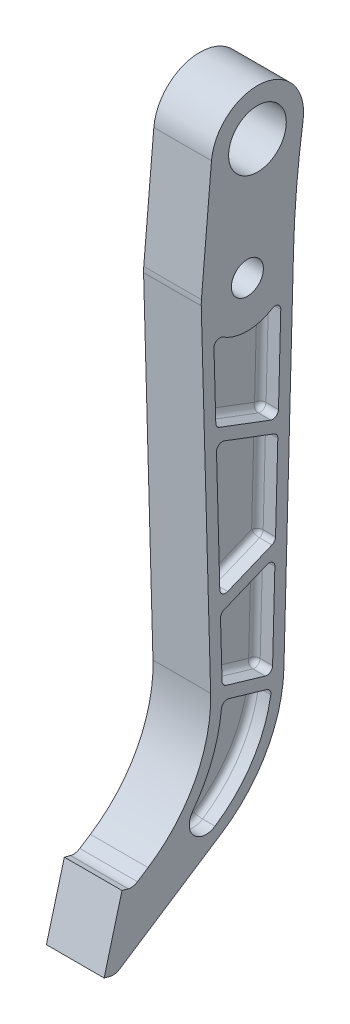
SolidWorks part; units mm, degrees
ref_plane "Front Plane" through (0, 0, 0) normal (0, 0, 1) x (1, 0, 0)
ref_plane "Top Plane" through (0, 0, 0) normal (0, 1, 0) x (1, 0, 0)
ref_plane "Right Plane" through (0, 0, 0) normal (1, 0, 0) x (0, 0, -1)
sketch "Sketch1" plane through (0, 0, 0) normal (1, 0, 0) x (0, 0, -1)
  line L0 (-25.3903, -0.7003) -> (-20.2239, -188.0148)
  line L1 (25.4, 0) -> (20.123, -196.1257)
  line L2 (0, 0) -> (-78.888, -294.4142) construction
  line L3 (0, 0) -> (0, -294.4142) construction
  line L4 (0, -294.4142) -> (-78.888, -294.4142) construction
  line L5 (-60.5169, -257.7014) -> (-54.6821, -253.8847)
  line L6 (-78.888, -294.4142) -> (-75.4975, -295.3227)
  line L7 (-78.888, -294.4142) -> (-69.027, -257.6124)
  line L8 (-69.027, -257.6124) -> (-65.6365, -258.5209)
  line L9 (-72.7544, -296.0577) -> (-62.8934, -259.2559) construction
  line L10 (-70.3779, -294.5031) -> (-14.3366, -257.8451)
  line L11 (0, 0) -> (5.5555, 63.5) construction
  line L12 (0, 0) -> (25.4, 0) construction
  line L13 (5.5555, 63.5) -> (5.5555, 0) construction
  line L14 (-19.7478, 65.7138) -> (-25.3033, 2.2138)
  circle A0 centre (0, 0) radius 8.8004
  arc A2 (-54.6821, -253.8847) -> (-20.2239, -188.0148) centre (-96.395, -190.1158) ccw
  arc A3 (-14.3366, -257.8451) -> (20.123, -196.1257) centre (-56.0494, -194.0762) ccw
  arc A4 (-70.3779, -294.5031) -> (-75.4975, -295.3227) centre (-73.854, -289.1891) cw
  arc A5 (-60.5169, -257.7014) -> (-65.6365, -258.5209) centre (-63.993, -252.3873) cw
  arc A8 (30.6732, 59.7236) -> (25.4, 0) centre (515.6373, -13.1904) ccw
  arc A9 (30.6732, 59.7236) -> (-19.7478, 65.7138) centre (5.5555, 63.5) ccw
  circle A10 centre (5.5555, 63.5) radius 15.875
  arc A11 (-25.3033, 2.2138) -> (-25.3903, -0.7003) centre (0, 0) ccw
  point P17 (-19.05, -230.5769)
  point P20 (19.05, -236.0062)
  dimension "D1" = 17.6007
  dimension "D2" = 25.4
  dimension "D7" = 76.2
  dimension "D8" = 76.2
  dimension "D12" = 6.35
  dimension "D13" = 6.35
  dimension "D14" = 25.4
  dimension "D17" = 31.75
  dimension "D3" = 304.8
  dimension "D4" = 15
  dimension "D5" = 38.1
  dimension "D6" = 6.35
  dimension "D9" = 19.05
  dimension "D10" = 19.05
  dimension "D11" = 25.4
  dimension "D15" = 5
  dimension "D16" = 63.5
  dimension "D18" = 25.4
extrude "Boss-Extrude1" add sketch "Sketch1" along normal mid plane 31.75
sketch "Sketch2" plane through (15.875, 0, 0) normal (1, 0, 0) x (0, 0, -1)
  line L0 (-11.6603, -188.4901) -> (9.8183, -194.7936)
  line L1 (-18.3877, -24.2757) -> (18.3947, -24.2692) construction
  line L2 (0.0035, -24.2725) -> (-0.921, -191.6419) construction
  line L3 (-16.082, -107.8709) -> (16.1405, -108.0489) construction
  line L4 (15.5153, -131.2875) -> (16.7658, -84.8102)
  line L5 (-15.1742, -141.2921) -> (-16.9898, -74.4496)
  line L6 (-10.7935, -144.1426) -> (13.5483, -134.1388)
  line L7 (-12.6932, -71.3935) -> (14.7147, -81.7549)
  line L8 (-15.3313, -63.6076) -> (12.8308, -74.2541)
  line L9 (-14.77, -63.8198) -> (19.139, -76.6389) construction
  line L10 (-18.3877, -24.2757) -> (-17.3823, -60.7253)
  line L11 (17.1274, -71.3697) -> (18.3947, -24.2692)
  line L12 (-12.8189, -151.8403) -> (10.761, -142.1497)
  line L13 (-12.9293, -151.8857) -> (17.6096, -139.3351) construction
  line L14 (-14.7858, -154.8646) -> (-13.94, -185.5312)
  line L15 (13.8862, -191.8325) -> (15.1417, -145.1717)
  line L16 (-19.0428, -0.5252) -> (-13.8763, -187.8398)
  line L17 (-51.206, -259.1988) -> (-57.0408, -263.0155)
  line L18 (-64.4537, -265.0789) -> (-70.2892, -286.8572)
  line L19 (-70.2892, -286.8572) -> (-17.8126, -252.5311)
  line L20 (13.7753, -195.9549) -> (19.0523, 0.1708)
  line L21 (-13.422, 65.1603) -> (-18.9775, 1.6603)
  line L22 (-18.3877, -24.2757) -> (-13.8763, -187.8398) construction
  line L26 (13.7753, -195.9549) -> (18.3947, -24.2692) construction
  line L28 (-15.3431, -146.0124) -> (15.1958, -133.4617) construction
  line L29 (-17.0155, -69.7595) -> (16.8936, -82.5786) construction
  line L30 (-10.1952, -195.5379) -> (10.6667, -201.6604)
  line L31 (-13.4485, -194.5832) -> (8.0301, -200.8866) construction
  arc A0 (-30.1717, -239.4004) -> (-17.8126, -252.5311) centre (-22.8255, -244.8676) ccw
  arc A1 (9.8183, -194.7936) -> (13.8862, -191.8325) centre (10.7124, -191.7471) ccw
  arc A2 (-11.6603, -188.4901) -> (-13.94, -185.5312) centre (-10.7662, -185.4436) cw
  arc A3 (-12.8189, -151.8403) -> (-14.7858, -154.8646) centre (-11.6121, -154.777) ccw
  arc A4 (10.761, -142.1497) -> (15.1417, -145.1717) centre (11.9678, -145.0863) cw
  arc A5 (15.5153, -131.2875) -> (13.5483, -134.1388) centre (12.3414, -131.2021) cw
  arc A6 (-15.1742, -141.2921) -> (-10.7935, -144.1426) centre (-12.0004, -141.2059) ccw
  arc A8 (-13.5235, -21.5006) -> (13.5297, -21.4967) centre (0, 0) ccw
  arc A9 (-25.3033, 2.2138) -> (-25.3903, -0.7003) centre (0, 0) ccw construction
  arc A10 (18.3947, -24.2692) -> (13.5297, -21.4967) centre (15.2209, -24.1838) ccw
  arc A11 (-18.3877, -24.2757) -> (-13.5235, -21.5006) centre (-15.2139, -24.1882) cw
  arc A14 (-18.9775, 1.6603) -> (-19.0428, -0.5252) centre (0, 0) ccw
  arc A15 (-51.206, -259.1988) -> (-13.8763, -187.8398) centre (-96.395, -190.1158) ccw
  arc A16 (-64.4537, -265.0789) -> (-57.0408, -263.0155) centre (-63.993, -252.3873) ccw
  arc A17 (-17.8126, -252.5311) -> (13.7753, -195.9549) centre (-56.0494, -194.0762) ccw
  arc A18 (24.3938, 60.6677) -> (19.0523, 0.1708) centre (515.6373, -13.1904) ccw
  arc A19 (24.3938, 60.6677) -> (-13.422, 65.1603) centre (5.5555, 63.5) ccw
  arc A21 (-30.1717, -239.4004) -> (-13.8763, -187.8398) centre (-96.395, -190.1158) ccw construction
  arc A23 (-17.8126, -252.5311) -> (13.7753, -195.9549) centre (-56.0494, -194.0762) ccw construction
  arc A24 (16.7658, -84.8102) -> (14.7147, -81.7549) centre (13.5919, -84.7248) ccw
  arc A25 (-12.6932, -71.3935) -> (-16.9898, -74.4496) centre (-13.8159, -74.3634) ccw
  arc A26 (12.8308, -74.2541) -> (17.1274, -71.3697) centre (13.9536, -71.2843) ccw
  arc A27 (-15.3313, -63.6076) -> (-17.3823, -60.7253) centre (-14.2086, -60.6377) cw
  arc A28 (-14.2488, -198.2708) -> (-30.1717, -239.4004) centre (-96.395, -190.1158) cw
  arc A29 (12.907, -205.2132) -> (-17.8126, -252.5311) centre (-56.0494, -194.0762) cw
  arc A30 (10.6667, -201.6604) -> (12.907, -205.2132) centre (9.7727, -204.7069) cw
  arc A31 (-10.1952, -195.5379) -> (-14.2488, -198.2708) centre (-11.0893, -198.5844) ccw
  point P14 (-0.4587, -107.9572)
  point P21 (16.1405, -108.0489)
  point P25 (-16.082, -107.8709)
  point P48 (-14.8463, -152.6735)
  point P52 (15.2729, -140.2954)
  point P63 (15.4597, -133.3533)
  point P70 (16.8265, -82.5533)
  point P76 (17.0073, -75.833)
  point P79 (-17.3236, -62.8544)
  point P86 (13.2989, -202.4329)
  point P89 (-13.958, -194.4336)
  dimension "D2" = 3.175
  dimension "D3" = 9.1573
  dimension "D8" = 3.175
  dimension "D11" = 3.175
  dimension "D4" = 13.5766
  dimension "D5" = 66.8426
  dimension "D6" = 6.35
  dimension "D7" = 6.35
  dimension "D9" = 46.4774
  dimension "D10" = 6.35
  dimension "D1" = 6.35
extrude "Cut-Extrude1" cut sketch "Sketch2" against normal blind 10
fillet "Fillet1" radius 3.175 30 edges at (5.875, -195.9518, 12.8641) (5.875, -198.5992, -0.2358) (5.875, -203.0134, -12.4583) (5.875, -232.1114, -2.5368) (5.875, -251.144, 29.4936) (5.875, -219.9187, 19.4126) (5.875, -191.6419, 0.921) (5.875, -187.3814, 13.2813) (5.875, -170.1979, 14.3629) (5.875, -153.046, 14.2736) (5.875, -146.995, 1.029) (5.875, -142.4729, -13.7708) (5.875, -168.5021, -14.514) (5.875, -194.314, -12.5809) (5.875, -139.1407, -1.3774) (5.875, -143.8672, 13.732) (5.875, -107.8709, 16.082) (5.875, -71.7761, 15.6562) (5.875, -76.5742, -1.0107) (5.875, -82.9551, -16.228) (5.875, -108.0489, -16.1405) (5.875, -133.005, -14.9549) (5.875, -47.8194, -17.7611) (5.875, -73.9203, -15.7233) (5.875, -68.9309, 1.2502) (5.875, -62.4785, 16.7954) (5.875, -42.5005, 17.885) (5.875, -21.4304, 16.7872) (5.875, -25.4, -0.0037) (5.875, -21.4253, -16.7929)
mirror "Mirror2" about plane through (0, 0, 0) normal (1, 0, 0) of "Fillet1", "Cut-Extrude1"
